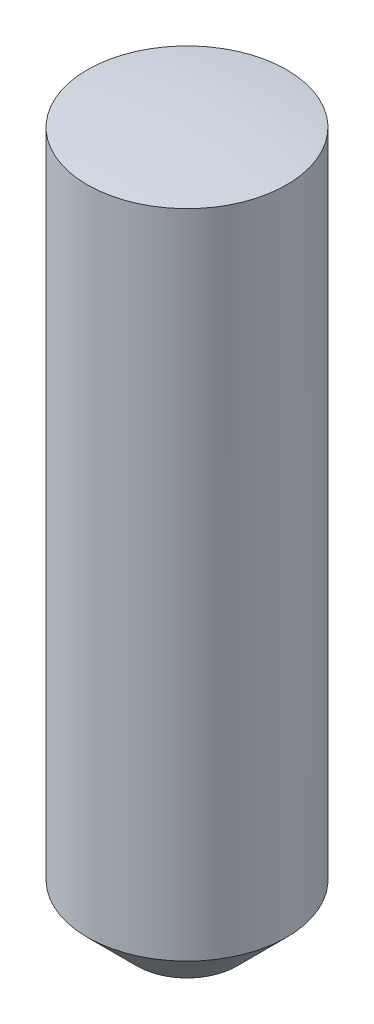
SolidWorks part; units mm, degrees
ref_plane "Front Plane" through (0, 0, 0) normal (0, 0, 1) x (1, 0, 0)
ref_plane "Top Plane" through (0, 0, 0) normal (0, 1, 0) x (1, 0, 0)
ref_plane "Right Plane" through (0, 0, 0) normal (1, 0, 0) x (0, 0, -1)
sketch "Sketch1" plane through (0, 0, 0) normal (0, 1, 0) x (1, 0, 0)
  circle A0 centre (0, 0) radius 1
  dimension "D1" = 2
extrude "Boss-Extrude 7.10mm" add sketch "Sketch1" against normal blind 7.1
chamfer "0.5 x 45 deg" distance 0.5 angle 45 1 edges at (0, -7.1, 1)
sketch "Sketch2" plane through (0, 0, 0) normal (0, 0, 1) x (1, 0, 0)
  line L0 (0, 0) -> (0, 2) construction
  line L1 (0, 2) -> (-2, 2)
  line L2 (-2, 2) -> (-2, -0.254)
  line L3 (0, 0) -> (0, 2)
  arc A0 (0, 0) -> (-2, -0.254) centre (0, -8) ccw
  dimension "D3" = 8
  dimension "D1" = 2
  dimension "D2" = 2
revolve "SR8" cut sketch "Sketch2" angle 360 about L0
